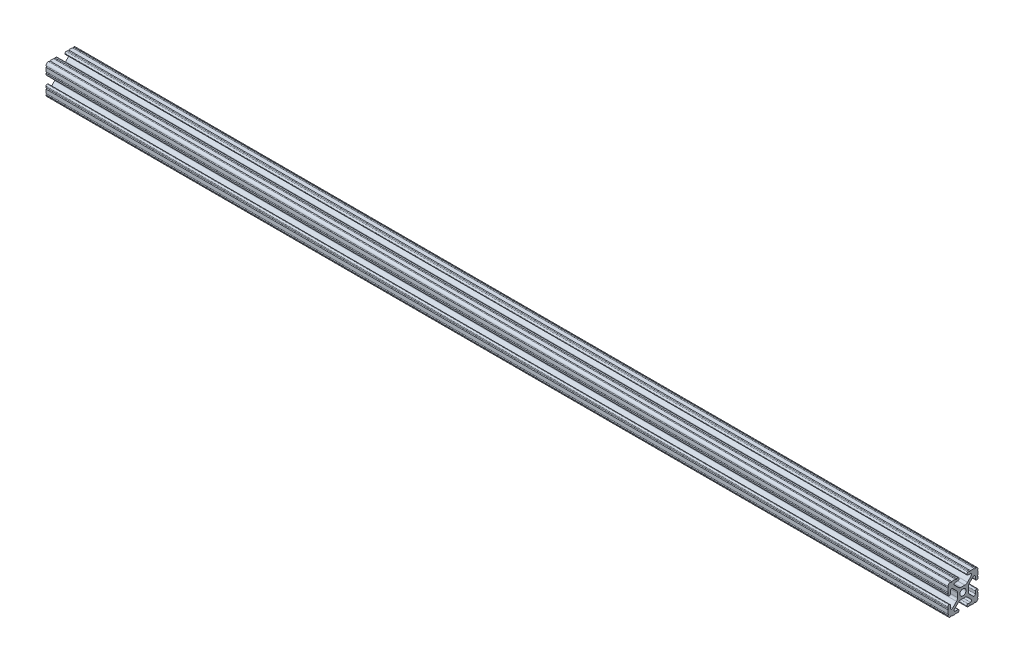
SolidWorks part; units mm, degrees
ref_plane "Front Plane" through (0, 0, 0) normal (0, 0, 1) x (1, 0, 0)
ref_plane "Top Plane" through (0, 0, 0) normal (0, 1, 0) x (1, 0, 0)
ref_plane "Right Plane" through (0, 0, 0) normal (1, 0, 0) x (0, 0, -1)
sketch "Sketch1" plane through (0, 0, 0) normal (0, 0, 1) x (1, 0, 0)
  line L0 (0, 0) -> (760, 0)
  dimension "D1" = 760
other "Extrusion 1010 PROFILE(1)"
ref_plane "Plane1" through (0, 0, 0) normal (1, 0, 0) x (0, 1, 0)
sketch "Sketch11" plane through (0, 0, 0) normal (1, 0, 0) x (0, 1, 0)
  line L1 (12.7, 12.7) -> (-12.7, 12.7) construction
  line L2 (12.7, 12.7) -> (12.7, -12.7) construction
  line L3 (12.7, -12.7) -> (-12.7, -12.7) construction
  line L4 (-12.7, 12.7) -> (-12.7, -12.7) construction
  line L5 (12.7, 12.7) -> (-12.7, -12.7) construction
  line L6 (12.7, -12.7) -> (-12.7, 12.7) construction
  line L88 (-1.7093, -4.4958) -> (1.7093, -4.4958)
  line L89 (3.9523, -5.4237) -> (7.1797, -8.6452)
  line L90 (6.4164, -10.4902) -> (4.2875, -10.4902)
  line L91 (3.2385, -11.5392) -> (3.2385, -11.651)
  line L92 (4.2875, -12.7) -> (5.3171, -12.7)
  line L93 (6.3331, -12.7) -> (9.5504, -12.7)
  line L94 (12.7, -9.5504) -> (12.7, -6.3331)
  line L95 (12.7, -5.3171) -> (12.7, -4.2875)
  line L96 (11.651, -3.2385) -> (11.5392, -3.2385)
  line L97 (10.4902, -4.2875) -> (10.4902, -6.4021)
  line L98 (8.737, -7.1292) -> (5.4405, -3.8388)
  line L99 (4.5085, -1.5917) -> (4.5085, 1.5917)
  line L100 (5.4405, 3.8388) -> (8.737, 7.1292)
  line L101 (10.4902, 6.4021) -> (10.4902, 4.2875)
  line L102 (11.5392, 3.2385) -> (11.651, 3.2385)
  line L103 (12.7, 4.2875) -> (12.7, 5.3171)
  line L104 (12.7, 6.3331) -> (12.7, 9.5504)
  line L105 (9.5504, 12.7) -> (6.3331, 12.7)
  line L106 (5.3171, 12.7) -> (4.2875, 12.7)
  line L107 (3.2384, 11.651) -> (3.2384, 11.5392)
  line L108 (4.2875, 10.4902) -> (6.4768, 10.4902)
  line L109 (7.2072, 8.7245) -> (3.9003, 5.4237)
  line L110 (1.6573, 4.4958) -> (-1.6573, 4.4958)
  line L111 (-3.9003, 5.4237) -> (-7.2072, 8.7245)
  line L112 (-6.4768, 10.4902) -> (-4.2875, 10.4902)
  line L113 (-3.2384, 11.5392) -> (-3.2384, 11.651)
  line L114 (-4.2875, 12.7) -> (-5.3171, 12.7)
  line L115 (-6.3331, 12.7) -> (-9.5504, 12.7)
  line L116 (-12.7, 9.5504) -> (-12.7, 6.3331)
  line L117 (-12.7, 5.3171) -> (-12.7, 4.2875)
  line L118 (-11.651, 3.2385) -> (-11.5392, 3.2385)
  line L119 (-10.4902, 4.2875) -> (-10.4902, 6.4021)
  line L120 (-8.737, 7.1292) -> (-5.4405, 3.8388)
  line L121 (-4.5085, 1.5917) -> (-4.5085, -1.5917)
  line L122 (-5.4405, -3.8388) -> (-8.737, -7.1292)
  line L123 (-10.4902, -6.4021) -> (-10.4902, -4.2875)
  line L124 (-11.5392, -3.2385) -> (-11.651, -3.2385)
  line L125 (-12.7, -4.2875) -> (-12.7, -5.3171)
  line L126 (-12.7, -6.3331) -> (-12.7, -9.5504)
  line L127 (-9.5504, -12.7) -> (-6.3331, -12.7)
  line L128 (-5.3171, -12.7) -> (-4.2875, -12.7)
  line L129 (-3.2385, -11.651) -> (-3.2385, -11.5392)
  line L130 (-4.2875, -10.4902) -> (-6.4164, -10.4902)
  line L131 (-7.1797, -8.6452) -> (-3.9523, -5.4237)
  circle A1 centre (0, 0) radius 2.6035
  arc A104 (-1.7093, -4.4958) -> (-3.9523, -5.4237) centre (-1.7093, -7.6708) ccw
  arc A105 (3.9523, -5.4237) -> (1.7093, -4.4958) centre (1.7093, -7.6708) ccw
  arc A106 (6.4164, -10.4902) -> (7.1797, -8.6452) centre (6.4164, -9.4098) ccw
  arc A107 (4.2875, -10.4902) -> (3.2385, -11.5392) centre (4.2875, -11.5392) ccw
  arc A108 (3.2385, -11.651) -> (4.2875, -12.7) centre (4.2875, -11.651) ccw
  arc A109 (6.3331, -12.7) -> (5.3171, -12.7) centre (5.8251, -12.7) ccw
  arc A110 (10.5664, -12.6998) -> (9.5504, -12.7) centre (10.0584, -12.7) ccw
  arc A111 (10.5664, -12.6998) -> (12.6998, -10.5664) centre (10.5918, -10.5918) ccw
  arc A112 (12.7, -9.5504) -> (12.6998, -10.5664) centre (12.7, -10.0584) ccw
  arc A113 (12.7, -5.3171) -> (12.7, -6.3331) centre (12.7, -5.8251) ccw
  arc A114 (12.7, -4.2875) -> (11.651, -3.2385) centre (11.651, -4.2875) ccw
  arc A115 (11.5392, -3.2385) -> (10.4902, -4.2875) centre (11.5392, -4.2875) ccw
  arc A116 (8.737, -7.1292) -> (10.4902, -6.4021) centre (9.4628, -6.4021) ccw
  arc A117 (4.5085, -1.5917) -> (5.4405, -3.8388) centre (7.6835, -1.5917) ccw
  arc A118 (5.4405, 3.8388) -> (4.5085, 1.5917) centre (7.6835, 1.5917) ccw
  arc A119 (10.4902, 6.4021) -> (8.737, 7.1292) centre (9.4628, 6.4021) ccw
  arc A120 (10.4902, 4.2875) -> (11.5392, 3.2385) centre (11.5392, 4.2875) ccw
  arc A121 (11.651, 3.2385) -> (12.7, 4.2875) centre (11.651, 4.2875) ccw
  arc A122 (12.7, 6.3331) -> (12.7, 5.3171) centre (12.7, 5.8251) ccw
  arc A123 (12.6998, 10.5664) -> (12.7, 9.5504) centre (12.7, 10.0584) ccw
  arc A124 (12.6998, 10.5664) -> (10.5664, 12.6998) centre (10.5918, 10.5918) ccw
  arc A125 (9.5504, 12.7) -> (10.5664, 12.6998) centre (10.0584, 12.7) ccw
  arc A126 (5.3171, 12.7) -> (6.3331, 12.7) centre (5.8251, 12.7) ccw
  arc A127 (4.2875, 12.7) -> (3.2384, 11.651) centre (4.2875, 11.651) ccw
  arc A128 (3.2384, 11.5392) -> (4.2875, 10.4902) centre (4.2875, 11.5392) ccw
  arc A129 (7.2072, 8.7245) -> (6.4768, 10.4902) centre (6.4768, 9.4563) ccw
  arc A130 (1.6573, 4.4958) -> (3.9003, 5.4237) centre (1.6573, 7.6708) ccw
  arc A131 (-3.9003, 5.4237) -> (-1.6573, 4.4958) centre (-1.6573, 7.6708) ccw
  arc A132 (-6.4768, 10.4902) -> (-7.2072, 8.7245) centre (-6.4768, 9.4563) ccw
  arc A133 (-4.2875, 10.4902) -> (-3.2384, 11.5392) centre (-4.2875, 11.5392) ccw
  arc A134 (-3.2384, 11.651) -> (-4.2875, 12.7) centre (-4.2875, 11.651) ccw
  arc A135 (-6.3331, 12.7) -> (-5.3171, 12.7) centre (-5.8251, 12.7) ccw
  arc A136 (-10.5664, 12.6998) -> (-9.5504, 12.7) centre (-10.0584, 12.7) ccw
  arc A137 (-10.5664, 12.6998) -> (-12.6998, 10.5664) centre (-10.5918, 10.5918) ccw
  arc A138 (-12.7, 9.5504) -> (-12.6998, 10.5664) centre (-12.7, 10.0584) ccw
  arc A139 (-12.7, 5.3171) -> (-12.7, 6.3331) centre (-12.7, 5.8251) ccw
  arc A140 (-12.7, 4.2875) -> (-11.651, 3.2385) centre (-11.651, 4.2875) ccw
  arc A141 (-11.5392, 3.2385) -> (-10.4902, 4.2875) centre (-11.5392, 4.2875) ccw
  arc A142 (-8.737, 7.1292) -> (-10.4902, 6.4021) centre (-9.4628, 6.4021) ccw
  arc A143 (-4.5085, 1.5917) -> (-5.4405, 3.8388) centre (-7.6835, 1.5917) ccw
  arc A144 (-5.4405, -3.8388) -> (-4.5085, -1.5917) centre (-7.6835, -1.5917) ccw
  arc A145 (-10.4902, -6.4021) -> (-8.737, -7.1292) centre (-9.4628, -6.4021) ccw
  arc A146 (-10.4902, -4.2875) -> (-11.5392, -3.2385) centre (-11.5392, -4.2875) ccw
  arc A147 (-11.651, -3.2385) -> (-12.7, -4.2875) centre (-11.651, -4.2875) ccw
  arc A148 (-12.7, -6.3331) -> (-12.7, -5.3171) centre (-12.7, -5.8251) ccw
  arc A149 (-12.6998, -10.5664) -> (-12.7, -9.5504) centre (-12.7, -10.0584) ccw
  arc A150 (-12.6998, -10.5664) -> (-10.5664, -12.6998) centre (-10.5918, -10.5918) ccw
  arc A151 (-9.5504, -12.7) -> (-10.5664, -12.6998) centre (-10.0584, -12.7) ccw
  arc A152 (-5.3171, -12.7) -> (-6.3331, -12.7) centre (-5.8251, -12.7) ccw
  arc A153 (-4.2875, -12.7) -> (-3.2385, -11.651) centre (-4.2875, -11.651) ccw
  arc A154 (-3.2385, -11.5392) -> (-4.2875, -10.4902) centre (-4.2875, -11.5392) ccw
  arc A155 (-7.1797, -8.6452) -> (-6.4164, -10.4902) centre (-6.4164, -9.4098) ccw
  point P3 (0, 0)
  point P21 (-12.7, 0)
  point P22 (0, 12.7)
  point P25 (12.7, 0)
  point P28 (0, -12.7)
  point P30 (-12.7, -12.7)
  point P33 (12.7, -12.7)
  point P37 (12.7, 12.7)
  point P40 (-12.7, 12.7)
  point P43 (0, 0)
  dimension "D1" = 25.4
